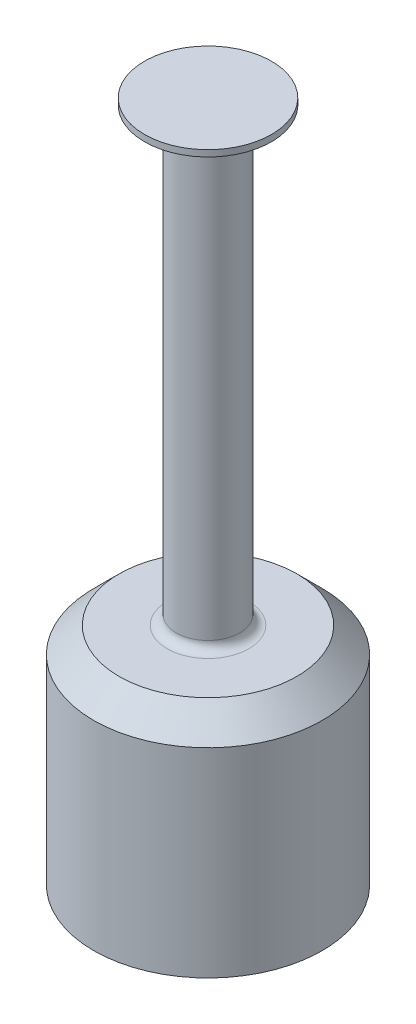
SolidWorks part; units mm, degrees
ref_plane "Front Plane" through (0, 0, 0) normal (0, 0, 1) x (1, 0, 0)
ref_plane "Top Plane" through (0, 0, 0) normal (0, 1, 0) x (1, 0, 0)
ref_plane "Right Plane" through (0, 0, 0) normal (1, 0, 0) x (0, 0, -1)
sketch "Sketch1" plane through (0, 0, 0) normal (0, 0, 1) x (1, 0, 0)
  line L0 (4.5, 9) -> (0, 9)
  line L1 (0, 9) -> (0, 0.15)
  line L2 (0, 0.15) -> (4.5, 0.15)
  line L3 (4.5, 0.15) -> (4.5, 9)
  line L4 (0, 9) -> (0, 0.15) construction
revolve "Revolve1" add sketch "Sketch1" angle 360 about L4
hole_wizard "Ø5.2 (5.2) Diameter Hole1" positions "Sketch3" profile "Sketch2" hole size "Ø5.2" standard "ANSI Metric"
sketch "Sketch3" plane through (0, 0.15, 0) normal (0, -1, 0) x (-1, 0, 0)
  point P0 (0, 0)
sketch "Sketch2" plane through (0, 0.15, 0) normal (1, 0, 0) x (0, 0, -1)
  line L0 (0, 0) -> (0, 8.35)
  line L1 (0, 8.35) -> (2.6, 8.35)
  line L2 (2.6, 8.35) -> (2.6, 0)
  line L5 (2.6, 0) -> (0, 0)
  line L10 (0, 8.35) -> (-2.6, 8.35) construction
  line L11 (0, -6.35) -> (0, 107.95) construction
  dimension "Hole Dia." = 5.2
  dimension "Hole Depth" = 8.35
  dimension "Drill Angle" = 180
sketch "Sketch4" plane through (0, 8.5, 0) normal (0, -1, 0) x (1, 0, 0)
  line L0 (-2, -1.6613) -> (2, -1.6613)
  arc A0 (2, -1.6613) -> (-2, -1.6613) centre (0, 0) cw
extrude "Boss-Extrude1" add sketch "Sketch4" along normal blind 5.98
sketch "Sketch5" plane through (0, 8.5, 0) normal (0, -1, 0) x (1, 0, 0)
  line L0 (2, 1.6613) -> (-2, 1.6613)
  arc A0 (-2, 1.6613) -> (2, 1.6613) centre (0, 0) cw
extrude "Boss-Extrude2" add sketch "Sketch5" along normal blind 5.98
sketch "Sketch6" plane through (0, 9, 0) normal (0, 1, 0) x (-1, 0, 0)
  circle A0 centre (0, 0) radius 1.25
extrude "Boss-Extrude3" add sketch "Sketch6" along normal blind 16.852
sketch "Sketch7" plane through (0, 25.852, 0) normal (0, 1, 0) x (-1, 0, 0)
  circle A0 centre (0, 0) radius 1.25
extrude "Boss-Extrude4" add sketch "Sketch7" along normal blind 0.8771 draft 54.944 draft outward yes
sketch "Sketch8" plane through (0, 26.7291, 0) normal (0, 1, 0) x (-1, 0, 0)
  circle A0 centre (0, 0) radius 2.5
extrude "Boss-Extrude5" add sketch "Sketch8" along normal blind 0.25
chamfer "Chamfer1" distance 1 angle 45 1 edges at (0, 9, -4.5)
fillet "Fillet1" radius 0.36 1 edges at (0, 9, 1.25)
